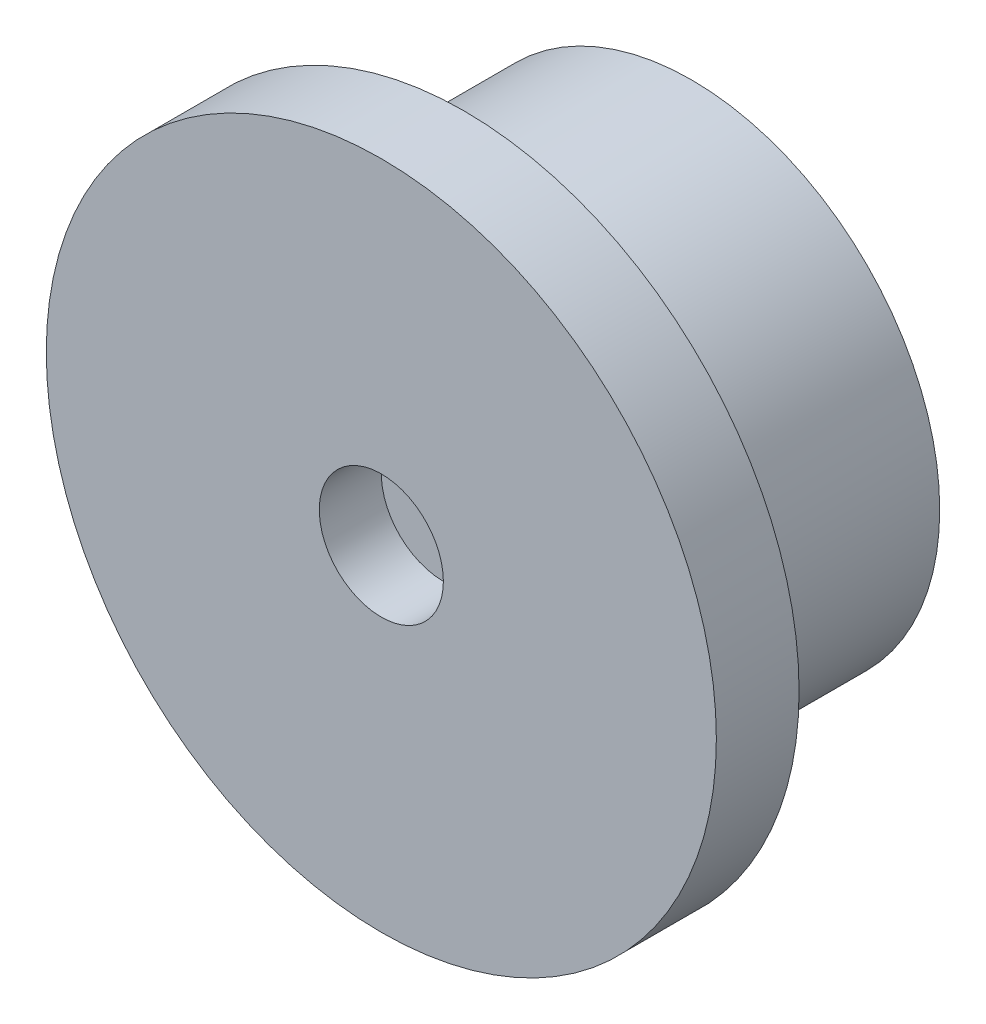
SolidWorks part; units mm, degrees
ref_plane "Ebene vorne" through (0, 0, 0) normal (0, 0, 1) x (1, 0, 0)
ref_plane "Ebene oben" through (0, 0, 0) normal (0, 1, 0) x (1, 0, 0)
ref_plane "Ebene rechts" through (0, 0, 0) normal (1, 0, 0) x (0, 0, -1)
sketch "Skizze1" plane through (0, 0, 0) normal (0, 0, 1) x (1, 0, 0)
  circle A0 centre (0, -12) radius 12
  circle A1 centre (0, -12) radius 12 construction
extrude "Aufsatz-Linear austragen1" add sketch "Skizze1" along normal up to surface (15 mm away)
sketch "Skizze2" plane through (0, 0, 15) normal (0, 0, 1) x (1, 0, 0)
  circle A0 centre (0, -12) radius 16.2
  circle A1 centre (0, -12) radius 16.2 construction
extrude "Aufsatz-Linear austragen3" add sketch "Skizze2" against normal up to surface (4 mm away) contours A0
sketch "Skizze3" plane through (0, 0, 0) normal (0, 0, 1) x (1, 0, 0)
  circle A0 centre (0, -12) radius 6
  dimension "D1" = 12
extrude "Schnitt-Linear austragen1" cut sketch "Skizze3" along normal blind 3
chamfer "Fase1" distance 1.5 angle 60 1 edges at (6, -12, 3)
sketch "Skizze4" plane through (0, 0, 15) normal (0, 0, 1) x (1, 0, 0)
  circle A0 centre (0, -12) radius 1.1
  circle A1 centre (0, -12) radius 16.2 construction
  dimension "D1" = 2.2
extrude "Schnitt-Linear austragen2" cut sketch "Skizze4" against normal through all
sketch "Skizze5" plane through (0, 0, 15) normal (0, 0, 1) x (1, 0, 0)
  circle A0 centre (0, -12) radius 3
  circle A1 centre (0, -12) radius 1.1 construction
  dimension "D1" = 6
extrude "Schnitt-Linear austragen3" cut sketch "Skizze5" against normal offset from surface (3 mm away) 9 up to face at (1.1, -12, 3)
